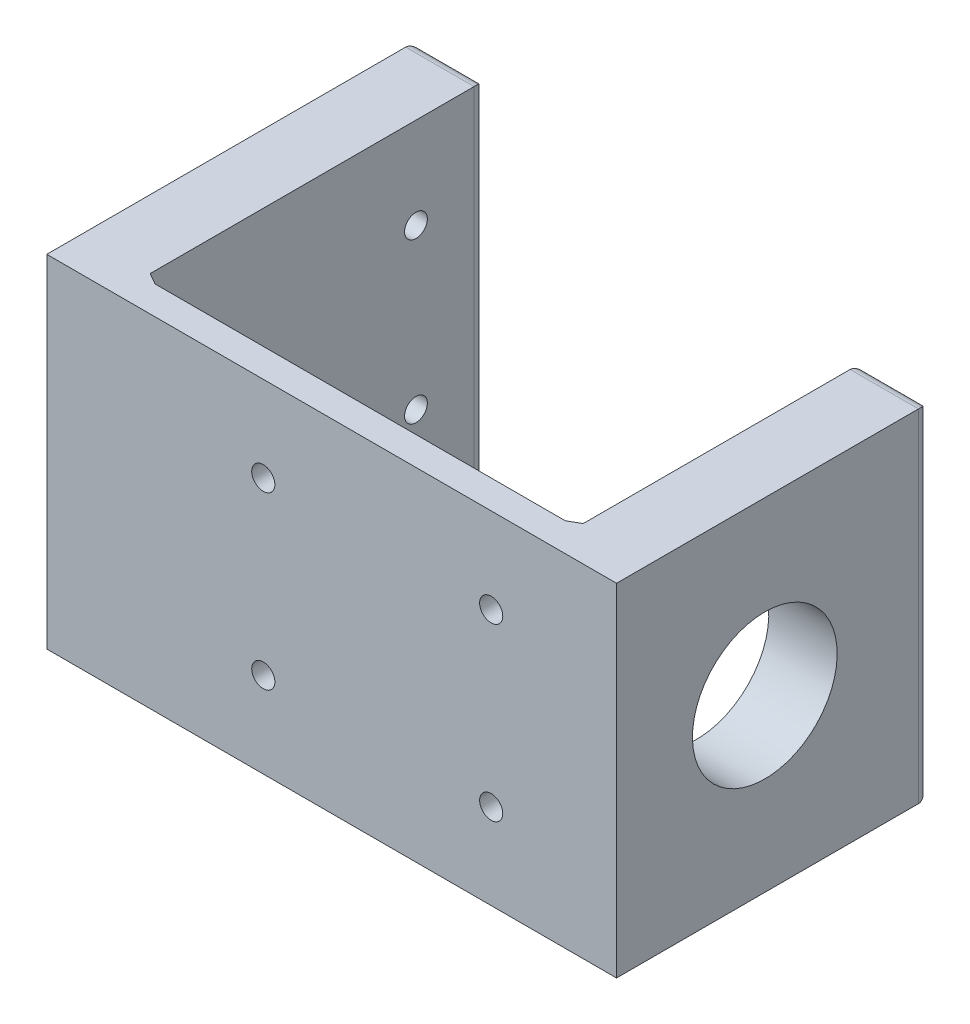
SolidWorks part; units mm, degrees
ref_plane "Front Plane" through (0, 0, 0) normal (0, 0, 1) x (1, 0, 0)
ref_plane "Top Plane" through (0, 0, 0) normal (0, 1, 0) x (1, 0, 0)
ref_plane "Right Plane" through (0, 0, 0) normal (1, 0, 0) x (0, 0, -1)
sketch "Sketch2" plane through (0, 0, 0) normal (0, 0, 1) x (1, 0, 0)
  line L1 (-127, 76.2) -> (0, 76.2)
  line L2 (-127, 76.2) -> (-127, 0)
  line L3 (-127, 0) -> (0, 0)
  line L4 (0, 76.2) -> (0, 0)
  point P0 (0, 0)
  point P23 (-63.5, 0)
  point P51 (-63.5, 76.2)
  dimension "D1" = 127
  dimension "D2" = 76.2
extrude "Boss-Extrude1" add sketch "Sketch2" along normal blind 6.35 contours L2 L1 L4 L3
hole_wizard "13/64 (0.20313) Diameter Hole1" positions "Sketch15" profile "Sketch16" hole size "13/64" standard "ANSI Inch" end condition through all
sketch "Sketch15" plane through (0, 0, 6.35) normal (0, 0, 1) x (1, 0, 0)
  line L0 (-78.74, 57.15) -> (-27.94, 57.15) construction
  line L3 (-27.94, 19.05) -> (-27.94, 0) construction
  line L4 (-127, 0) -> (0, 0) construction
  line L5 (-27.94, 57.15) -> (0, 57.15) construction
  line L6 (0, 76.2) -> (0, 0) construction
  line L8 (-127, 76.2) -> (-127, 0) construction
  line L9 (-78.74, 57.15) -> (-78.74, 19.05) construction
  point P0 (-78.74, 57.15)
  point P2 (-78.74, 19.05)
  point P4 (-27.94, 57.15)
  point P6 (-27.94, 19.05)
  point P53 (-127, 38.1)
  point P61 (-78.74, 38.1)
  dimension "D1" = 50.8
  dimension "D2" = 38.1
  dimension "D3" = 27.94
sketch "Sketch16" plane through (-78.74, 57.15, 6.35) normal (1, 0, 0) x (0, -1, 0)
  line L0 (0, 0) -> (0, 6.35)
  line L1 (0, 6.35) -> (2.5798, 6.35)
  line L2 (2.5798, 6.35) -> (2.5798, 0)
  line L5 (2.5798, 0) -> (0, 0)
  line L11 (0, -6.35) -> (0, 107.95) construction
  dimension "Thru Hole Dia." = 5.1595
  dimension "Thru Hole Depth" = 6.35
sketch "Sketch5" plane through (0, 0, 0) normal (0, 0, -1) x (-1, 0, 0)
  line L0 (0, 76.2) -> (0, 0) construction
  line L4 (0, 76.2) -> (15.24, 76.2)
  line L5 (0, 76.2) -> (0, 0)
  line L6 (0, 0) -> (15.24, 0)
  line L7 (15.24, 76.2) -> (15.24, 0)
  line L8 (0, 76.2) -> (15.24, 0) construction
  line L9 (0, 0) -> (15.24, 76.2) construction
  point P0 (7.62, 38.1)
  point P4 (0, 38.1)
  dimension "D1" = 7.62
  dimension "D2" = 15.24
  dimension "D3" = 76.2
extrude "Boss-Extrude2" add sketch "Sketch5" along normal blind 63.5
chamfer "Chamfer1" distance 2.54 angle 30 1 edges at (-15.24, 38.1, 0)
fillet "Fillet3" radius 2.54 4 edges at (-7.62, 0, -63.5) (-15.24, 38.1, -63.5) (-7.62, 76.2, -63.5) (0, 38.1, -63.5)
hole_wizard "5/16 (0.3125) Diameter Hole1" positions "Sketch7" profile "Sketch8" hole size "5/16" standard "ANSI Inch"
sketch "Sketch7" plane through (-15.24, 0, 0) normal (-1, 0, 0) x (0, 0, 1)
  point P7 (-24.5552, 38.1)
sketch "Sketch8" plane through (-15.24, 38.1, -24.5552) normal (0, 1, 0) x (0, 0, 1)
  line L0 (0, 0) -> (0, 15.24)
  line L1 (0, 15.24) -> (15.875, 15.24)
  line L2 (15.875, 15.24) -> (15.875, 0)
  line L5 (15.875, 0) -> (0, 0)
  line L11 (0, -6.35) -> (0, 107.95) construction
  dimension "Thru Hole Dia." = 31.75
  dimension "Thru Hole Depth" = 15.24
sketch "Sketch9" plane through (0, 0, 0) normal (0, 0, -1) x (-1, 0, 0)
  line L0 (127, 76.2) -> (127, 0) construction
  line L3 (111.76, 76.2) -> (127, 76.2)
  line L4 (111.76, 76.2) -> (111.76, 0)
  line L5 (111.76, 0) -> (127, 0)
  line L6 (127, 76.2) -> (127, 0)
  line L7 (111.76, 76.2) -> (127, 0) construction
  line L8 (111.76, 0) -> (127, 76.2) construction
  point P1 (119.38, 38.1)
  point P10 (127, 38.1)
  dimension "D1" = 7.62
  dimension "D2" = 15.24
  dimension "D3" = 76.2
extrude "Boss-Extrude3" add sketch "Sketch9" along normal blind 76.2
chamfer "Chamfer5" distance 2.54 angle 30 1 edges at (-111.76, 38.1, 0)
fillet "Fillet5" radius 2.54 4 edges at (-119.38, 0, -76.2) (-111.76, 38.1, -76.2) (-127, 38.1, -76.2) (-119.38, 76.2, -76.2)
sketch "Sketch17" plane through (-127, 0, 0) normal (-1, 0, 0) x (0, 0, 1)
  line L0 (6.35, 38.1) -> (-73.66, 38.1) construction
  line L1 (-12.7, 20.32) -> (-60.7, 20.32) construction
  line L2 (-12.7, 20.32) -> (-60.7, 20.32) construction
  line L3 (-12.7, 55.88) -> (-12.7, 20.32) construction
  line L4 (6.35, 76.2) -> (6.35, 0) construction
  line L5 (-73.66, 76.2) -> (-73.66, 0) construction
  line L6 (-12.7, 55.88) -> (-12.7, 20.32) construction
  circle A2 centre (-12.7, 20.32) radius 2.54
  circle A3 centre (-12.7, 55.88) radius 2.54
  circle A4 centre (-60.7, 20.32) radius 2.54
  circle A5 centre (-60.7, 55.88) radius 2.54
  circle A6 centre (-12.7, 20.32) radius 2.921 construction
  circle A7 centre (-12.7, 20.32) radius 2.921 construction
  circle A8 centre (-60.7, 20.32) radius 2.921 construction
  circle A9 centre (-60.7, 20.32) radius 2.921 construction
  circle A10 centre (-12.7, 55.88) radius 2.921 construction
  circle A11 centre (-12.7, 55.88) radius 2.921 construction
  dimension "D2" = 5.08
  dimension "D3" = 19.05
extrude "Cut-Extrude1" cut sketch "Sketch17" against normal up to next
sketch "Sketch18" plane through (0, 0, 0) normal (1, 0, 0) x (0, 0, -1)
  line L0 (-6.35, 38.1) -> (60.96, 38.1) construction
  line L1 (-6.35, 76.2) -> (-6.35, 0) construction
  line L2 (60.96, 0) -> (60.96, 76.2) construction
  circle A0 centre (26.7, 38.02) radius 16.129
  circle A1 centre (26.7, 38.02) radius 12.446 construction
  circle A2 centre (26.7, 38.02) radius 12.446 construction
  dimension "D1" = 32.258
extrude "Cut-Extrude2" cut sketch "Sketch18" against normal up to next
